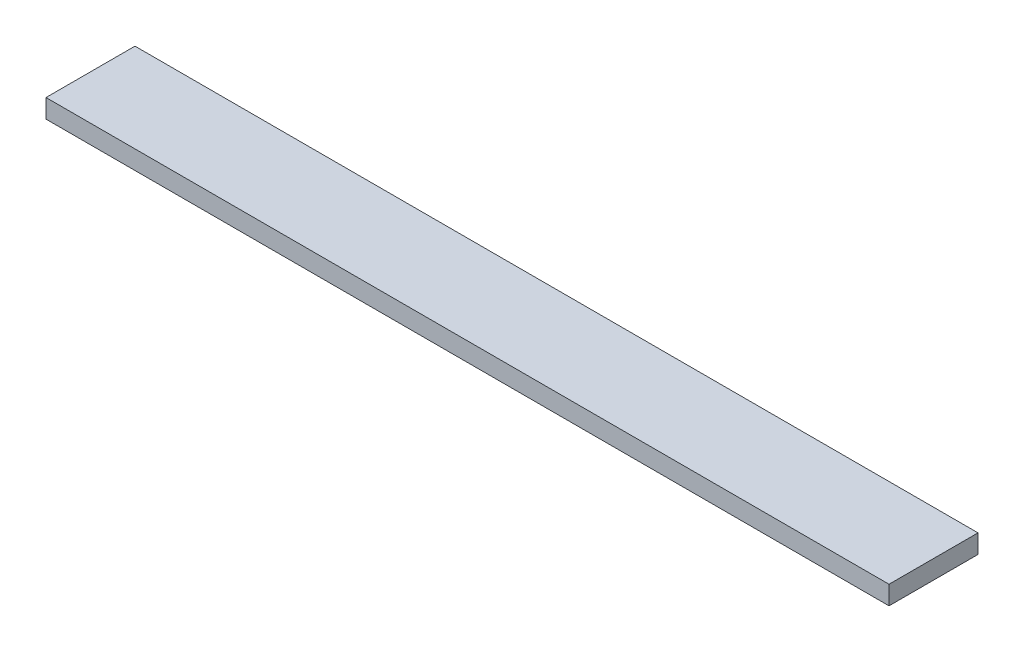
SolidWorks part; units mm, degrees
ref_plane "Front Plane" through (0, 0, 0) normal (0, 0, 1) x (1, 0, 0)
ref_plane "Top Plane" through (0, 0, 0) normal (0, 1, 0) x (1, 0, 0)
ref_plane "Right Plane" through (0, 0, 0) normal (1, 0, 0) x (0, 0, -1)
sketch "Sketch1" plane through (0, 0, 0) normal (0, 1, 0) x (1, 0, 0)
  line L1 (0, 0) -> (114.3, 0)
  line L2 (0, 0) -> (0, 12.065)
  line L3 (0, 12.065) -> (114.3, 12.065)
  line L4 (114.3, 0) -> (114.3, 12.065)
  dimension "D1" = 12.065
  dimension "D2" = 114.3
extrude "Boss-Extrude1" add sketch "Sketch1" along normal blind 2.54
